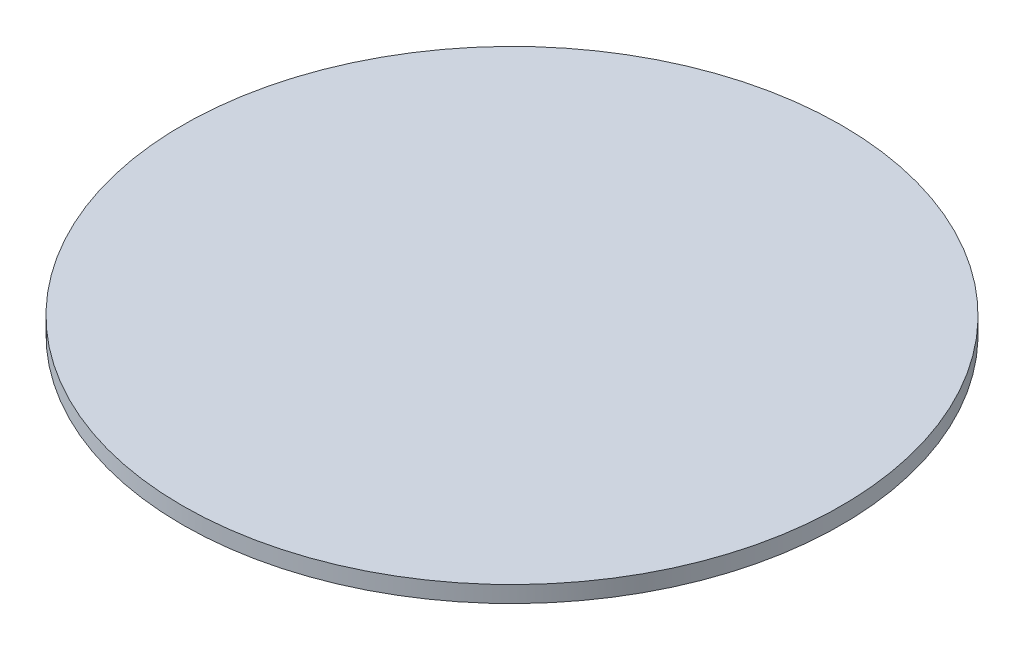
SolidWorks part; units mm, degrees
ref_plane "Face" through (0, 0, 0) normal (0, 0, 1) x (1, 0, 0)
ref_plane "Dessus" through (0, 0, 0) normal (0, 1, 0) x (1, 0, 0)
ref_plane "Droite" through (0, 0, 0) normal (1, 0, 0) x (0, 0, -1)
sketch "Esquisse1" plane through (0, 0, 0) normal (0, 1, 0) x (1, 0, 0)
  circle A0 centre (0, 0) radius 200
  dimension "D1" = 400
extrude "Extrusion1" add sketch "Esquisse1" along normal blind 10
